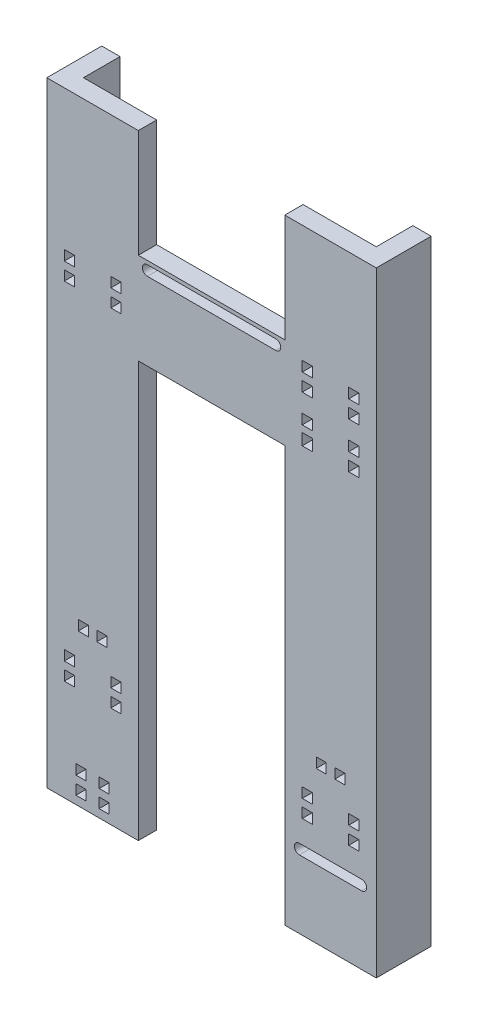
SolidWorks part; units mm, degrees
ref_plane "Front Plane" through (0, 0, 0) normal (0, 0, 1) x (1, 0, 0)
ref_plane "Top Plane" through (0, 0, 0) normal (0, 1, 0) x (1, 0, 0)
ref_plane "Right Plane" through (0, 0, 0) normal (1, 0, 0) x (0, 0, -1)
sketch "Sketch2" plane through (0, 0, 0) normal (0, 0, 1) x (1, 0, 0)
  line L1 (12.5, 84) -> (-12.5, 84)
  line L2 (12.5, 84) -> (12.5, -84)
  line L3 (12.5, -84) -> (-12.5, -84)
  line L4 (-12.5, 84) -> (-12.5, -84)
  line L5 (12.5, 84) -> (-12.5, -84) construction
  line L6 (12.5, -84) -> (-12.5, 84) construction
  point P0 (0, 0)
  dimension "D1" = 168
  dimension "D2" = 25
extrude "Boss-Extrude1" add sketch "Sketch2" along normal blind 5
sketch "Sketch3" plane through (-12.5, 0, 0) normal (-1, 0, 0) x (0, 0, 1)
  line L0 (5, -84) -> (0, -84) construction
  line L1 (0, 84) -> (-10, 84)
  line L2 (0, 84) -> (0, -84)
  line L3 (0, -84) -> (-10, -84)
  line L4 (-10, 84) -> (-10, -84)
  dimension "D1" = 10
  dimension "D2" = 0
extrude "Boss-Extrude2" add sketch "Sketch3" against normal blind 5
sketch "Sketch4" plane through (0, 0, 5) normal (0, 0, 1) x (1, 0, 0)
  line L0 (12.5, 0) -> (12.5, 84) construction
  line L1 (12.5, -84) -> (12.5, 84) construction
  line L2 (12.5, 54.5) -> (12.5, 29.5)
  line L4 (12.5, 54.5) -> (52.5, 54.5)
  line L5 (12.5, 54.5) -> (12.5, 29.5)
  line L6 (12.5, 29.5) -> (52.5, 29.5)
  line L7 (52.5, 54.5) -> (52.5, 29.5)
  point P8 (12.5, 42)
  line M5 (12.5, -84) -> (12.5, 84)
  dimension "D1" = 25
  dimension "D2" = 40
extrude "Boss-Extrude3" add sketch "Sketch4" against normal blind 5 contours L7 L4 L6 M5
sketch "Sketch5" plane through (0, 0, 5) normal (0, 0, 1) x (1, 0, 0)
  line L0 (52.5, 54.5) -> (52.5, 87.2525) construction
  line L2 (12.5, 84) -> (52.5, 84) construction
  line L3 (-12.5, -84) -> (12.5, -84) construction
  line L4 (52.5, 84) -> (77.5, 84)
  line L5 (52.5, 84) -> (52.5, -84)
  line L6 (52.5, -84) -> (77.5, -84)
  line L7 (77.5, 84) -> (77.5, -84)
  dimension "D1" = 25
  dimension "D2" = 0
extrude "Boss-Extrude4" add sketch "Sketch5" against normal blind 5
sketch "Sketch6" plane through (77.5, 0, 0) normal (1, 0, 0) x (0, 0, -1)
  line L0 (10, -84) -> (0, -84) construction
  line L1 (0, 84) -> (10, 84)
  line L2 (0, 84) -> (0, -84)
  line L3 (0, -84) -> (10, -84)
  line L4 (10, 84) -> (10, -84)
  line L5 (10, 84) -> (10, -84) construction
extrude "Boss-Extrude5" add sketch "Sketch6" against normal blind 5
sketch "Sketch7" plane through (0, 0, 5) normal (0, 0, 1) x (1, 0, 0)
  line L0 (14.9659, 52.125) -> (50.0341, 52.125) construction
  line L1 (14.9659, 53.5) -> (50.0341, 53.5)
  line L2 (14.9659, 50.75) -> (50.0341, 50.75)
  line L3 (12.5, 54.5) -> (52.5, 54.5) construction
  arc A0 (14.9659, 53.5) -> (14.9659, 50.75) centre (14.9659, 52.125) ccw
  arc A1 (50.0341, 50.75) -> (50.0341, 53.5) centre (50.0341, 52.125) ccw
  point P2 (32.5, 52.125)
  dimension "D1" = 2.75
  dimension "D2" = 1
extrude "Cut-Extrude1" cut sketch "Sketch7" against normal blind 5
sketch "Sketch8" plane through (0, 0, 5) normal (0, 0, 1) x (1, 0, 0)
  line L0 (73.5006, -64) -> (56.4994, -64) construction
  line L1 (73.5006, -65.375) -> (56.4994, -65.375)
  line L2 (73.5006, -62.625) -> (56.4994, -62.625)
  line L3 (52.5, -84) -> (77.5, -84) construction
  arc A0 (73.5006, -65.375) -> (73.5006, -62.625) centre (73.5006, -64) ccw
  arc A1 (56.4994, -62.625) -> (56.4994, -65.375) centre (56.4994, -64) ccw
  point P2 (65, -64)
  dimension "D1" = 2.75
  dimension "D2" = 20
extrude "Cut-Extrude2" cut sketch "Sketch8" against normal blind 20
sketch "Sketch9" plane through (0, 0, 5) normal (0, 0, 1) x (1, 0, 0)
  line L0 (12.5, 29.5) -> (12.5, 54.5) construction
  line L1 (12.5, 54.5) -> (12.5, 42) construction
  line L2 (12.5, 42) -> (-12.5, 42) construction
  line L3 (-12.5, 84) -> (-12.5, -84) construction
  line L4 (0, 42) -> (12.5, 42) construction
  line L5 (0, 42) -> (-12.5, 42) construction
  line L6 (12.5, 44.3813) -> (-12.5, 44.3813) construction
  line L7 (12.5, 39.6188) -> (-12.5, 39.6188) construction
  line L9 (7.725, 45.7563) -> (4.975, 45.7563)
  line L10 (7.725, 45.7563) -> (7.725, 43.0063)
  line L11 (7.725, 43.0063) -> (4.975, 43.0063)
  line L12 (4.975, 45.7563) -> (4.975, 43.0063)
  line L13 (7.725, 45.7563) -> (4.975, 43.0063) construction
  line L14 (7.725, 43.0063) -> (4.975, 45.7563) construction
  line L15 (-4.975, 45.7563) -> (-7.725, 45.7563)
  line L16 (-4.975, 45.7563) -> (-4.975, 43.0063)
  line L17 (-4.975, 43.0063) -> (-7.725, 43.0063)
  line L18 (-7.725, 45.7563) -> (-7.725, 43.0063)
  line L19 (-4.975, 45.7563) -> (-7.725, 43.0063) construction
  line L20 (-4.975, 43.0063) -> (-7.725, 45.7563) construction
  line L21 (-7.725, 40.9635) -> (-4.975, 40.9635)
  line L22 (-7.725, 40.9635) -> (-7.725, 38.274)
  line L23 (-7.725, 38.274) -> (-4.975, 38.274)
  line L24 (-4.975, 40.9635) -> (-4.975, 38.274)
  line L25 (-7.725, 40.9635) -> (-4.975, 38.274) construction
  line L26 (-7.725, 38.274) -> (-4.975, 40.9635) construction
  line L27 (4.975, 40.9635) -> (7.725, 40.9635)
  line L28 (4.975, 40.9635) -> (4.975, 38.274)
  line L29 (4.975, 38.274) -> (7.725, 38.274)
  line L30 (7.725, 40.9635) -> (7.725, 38.274)
  line L31 (4.975, 40.9635) -> (7.725, 38.274) construction
  line L32 (4.975, 38.274) -> (7.725, 40.9635) construction
  circle A0 centre (6.35, 39.6188) radius 1.375 construction
  circle A1 centre (-6.35, 39.6188) radius 1.375 construction
  circle A2 centre (6.35, 44.3813) radius 1.375 construction
  circle A3 centre (-6.35, 44.3813) radius 1.375 construction
  point P17 (0, 39.6188)
  dimension "D5" = 2.75
  dimension "D6" = 2.75
  dimension "D7" = 2.75
  dimension "D8" = 2.75
  dimension "D1" = 2.3813
  dimension "D2" = 2.3813
  dimension "D3" = 6.35
  dimension "D4" = 6.35
extrude "Cut-Extrude3" cut sketch "Sketch9" against normal blind 20
sketch "Sketch10" plane through (0, 0, 5) normal (0, 0, 1) x (1, 0, 0)
  line L0 (52.5, 54.5) -> (52.5, 29.5) construction
  line L1 (52.5, 29.5) -> (52.5, 42) construction
  line L2 (52.5, 42) -> (52.5, 35.75) construction
  line L3 (52.5, 35.75) -> (77.5, 35.75) construction
  line L4 (77.5, -84) -> (77.5, 84) construction
  line L5 (52.5, 54.5) -> (52.5, 42) construction
  line L6 (52.5, 42) -> (52.5, 48.25) construction
  line L7 (52.5, 48.25) -> (77.5, 48.25) construction
  line L8 (52.5, 50.6313) -> (77.5, 50.6313) construction
  line L9 (52.5, 45.8688) -> (77.5, 45.8688) construction
  line L10 (52.5, 38.1313) -> (77.5, 38.1313) construction
  line L11 (52.5, 33.3688) -> (77.5, 33.3688) construction
  line L14 (57.275, 52.0063) -> (60.025, 52.0063)
  line L15 (57.275, 52.0063) -> (57.275, 49.2563)
  line L16 (57.275, 49.2563) -> (60.025, 49.2563)
  line L17 (60.025, 52.0063) -> (60.025, 49.2563)
  line L18 (57.275, 52.0063) -> (60.025, 49.2563) construction
  line L19 (57.275, 49.2563) -> (60.025, 52.0063) construction
  line L20 (69.975, 52.0063) -> (72.725, 52.0063)
  line L21 (69.975, 52.0063) -> (69.975, 49.2563)
  line L22 (69.975, 49.2563) -> (72.725, 49.2563)
  line L23 (72.725, 52.0063) -> (72.725, 49.2563)
  line L24 (69.975, 52.0063) -> (72.725, 49.2563) construction
  line L25 (69.975, 49.2563) -> (72.725, 52.0063) construction
  line L26 (57.275, 47.2438) -> (60.025, 47.2438)
  line L27 (57.275, 47.2438) -> (57.275, 44.4938)
  line L28 (57.275, 44.4938) -> (60.025, 44.4938)
  line L29 (60.025, 47.2438) -> (60.025, 44.4938)
  line L30 (57.275, 47.2438) -> (60.025, 44.4938) construction
  line L31 (57.275, 44.4938) -> (60.025, 47.2438) construction
  line L32 (69.975, 47.2438) -> (72.725, 47.2438)
  line L33 (69.975, 47.2438) -> (69.975, 44.4938)
  line L34 (69.975, 44.4938) -> (72.725, 44.4938)
  line L35 (72.725, 47.2438) -> (72.725, 44.4938)
  line L36 (69.975, 47.2438) -> (72.725, 44.4938) construction
  line L37 (69.975, 44.4938) -> (72.725, 47.2438) construction
  line L38 (69.975, 39.5063) -> (72.725, 39.5063)
  line L39 (69.975, 39.5063) -> (69.975, 36.7563)
  line L40 (69.975, 36.7563) -> (72.725, 36.7563)
  line L41 (72.725, 39.5063) -> (72.725, 36.7563)
  line L42 (69.975, 39.5063) -> (72.725, 36.7563) construction
  line L43 (69.975, 36.7563) -> (72.725, 39.5063) construction
  line L44 (57.275, 39.5063) -> (60.025, 39.5063)
  line L45 (57.275, 39.5063) -> (57.275, 36.7563)
  line L46 (57.275, 36.7563) -> (60.025, 36.7563)
  line L47 (60.025, 39.5063) -> (60.025, 36.7563)
  line L48 (57.275, 39.5063) -> (60.025, 36.7563) construction
  line L49 (57.275, 36.7563) -> (60.025, 39.5063) construction
  line L50 (57.275, 34.9438) -> (60.025, 34.9438)
  line L51 (57.275, 34.9438) -> (57.275, 31.7938)
  line L52 (57.275, 31.7938) -> (60.025, 31.7938)
  line L53 (60.025, 34.9438) -> (60.025, 31.7938)
  line L54 (57.275, 34.9438) -> (60.025, 31.7938) construction
  line L55 (57.275, 31.7938) -> (60.025, 34.9438) construction
  line L56 (69.975, 34.7438) -> (72.725, 34.7438)
  line L57 (69.975, 34.7438) -> (69.975, 31.9938)
  line L58 (69.975, 31.9938) -> (72.725, 31.9938)
  line L59 (72.725, 34.7438) -> (72.725, 31.9938)
  line L60 (69.975, 34.7438) -> (72.725, 31.9938) construction
  line L61 (69.975, 31.9938) -> (72.725, 34.7438) construction
  circle A0 centre (71.35, 33.3688) radius 1.375 construction
  circle A1 centre (58.65, 33.3688) radius 1.375 construction
  circle A2 centre (58.65, 38.1313) radius 1.375 construction
  circle A3 centre (71.35, 38.1313) radius 1.375 construction
  circle A4 centre (71.35, 45.8688) radius 1.375 construction
  circle A5 centre (58.65, 45.8688) radius 1.375 construction
  circle A6 centre (58.65, 50.6313) radius 1.375 construction
  circle A7 centre (71.35, 50.6313) radius 1.375 construction
  point P23 (65, 33.3688)
  dimension "D7" = 2.75
  dimension "D8" = 2.75
  dimension "D9" = 2.75
  dimension "D10" = 2.75
  dimension "D11" = 2.75
  dimension "D12" = 2.75
  dimension "D13" = 2.75
  dimension "D14" = 2.75
  dimension "D1" = 2.3813
  dimension "D2" = 2.3813
  dimension "D3" = 2.3813
  dimension "D4" = 2.3813
  dimension "D5" = 6.35
  dimension "D6" = 6.35
extrude "Cut-Extrude4" cut sketch "Sketch10" against normal blind 20
sketch "Sketch11" plane through (0, 0, 5) normal (0, 0, 1) x (1, 0, 0)
  line L0 (-12.5, -52.625) -> (12.5, -52.625) construction
  line L1 (-12.5, 84) -> (-12.5, -84) construction
  line L2 (12.5, -84) -> (12.5, 29.5) construction
  line L3 (52.5, -52.625) -> (77.5, -52.625) construction
  line L4 (52.5, 29.5) -> (52.5, -84) construction
  line L5 (77.5, -84) -> (77.5, 84) construction
  line L6 (12.5, -50.2437) -> (-12.5, -50.2437) construction
  line L7 (-12.5, -55.0062) -> (12.5, -55.0062) construction
  line L8 (52.5, -55.0062) -> (77.5, -55.0062) construction
  line L9 (52.5, -50.2437) -> (77.5, -50.2437) construction
  line L10 (73.5006, -62.625) -> (56.4994, -62.625) construction
  line L12 (60.025, -48.8687) -> (57.275, -48.8687)
  line L13 (60.025, -48.8687) -> (60.025, -51.6187)
  line L14 (60.025, -51.6187) -> (57.275, -51.6187)
  line L15 (57.275, -48.8687) -> (57.275, -51.6187)
  line L16 (60.025, -48.8687) -> (57.275, -51.6187) construction
  line L17 (60.025, -51.6187) -> (57.275, -48.8687) construction
  line L18 (72.741, -48.8687) -> (69.959, -48.8687)
  line L19 (72.741, -48.8687) -> (72.741, -51.6187)
  line L20 (72.741, -51.6187) -> (69.959, -51.6187)
  line L21 (69.959, -48.8687) -> (69.959, -51.6187)
  line L22 (72.741, -48.8687) -> (69.959, -51.6187) construction
  line L23 (72.741, -51.6187) -> (69.959, -48.8687) construction
  line L24 (69.98, -53.6362) -> (72.72, -53.6362)
  line L25 (69.98, -53.6362) -> (69.98, -56.3762)
  line L26 (69.98, -56.3762) -> (72.72, -56.3762)
  line L27 (72.72, -53.6362) -> (72.72, -56.3762)
  line L28 (69.98, -53.6362) -> (72.72, -56.3762) construction
  line L29 (69.98, -56.3762) -> (72.72, -53.6362) construction
  line L30 (57.275, -53.6362) -> (60.025, -53.6362)
  line L31 (57.275, -53.6362) -> (57.275, -56.3762)
  line L32 (57.275, -56.3762) -> (60.025, -56.3762)
  line L33 (60.025, -53.6362) -> (60.025, -56.3762)
  line L34 (57.275, -53.6362) -> (60.025, -56.3762) construction
  line L35 (57.275, -56.3762) -> (60.025, -53.6362) construction
  line L36 (-7.725, -48.8687) -> (-4.975, -48.8687)
  line L37 (-7.725, -48.8687) -> (-7.725, -51.6187)
  line L38 (-7.725, -51.6187) -> (-4.975, -51.6187)
  line L39 (-4.975, -48.8687) -> (-4.975, -51.6187)
  line L40 (-7.725, -48.8687) -> (-4.975, -51.6187) construction
  line L41 (-7.725, -51.6187) -> (-4.975, -48.8687) construction
  line L42 (4.975, -48.8687) -> (7.725, -48.8687)
  line L43 (4.975, -48.8687) -> (4.975, -51.6187)
  line L44 (4.975, -51.6187) -> (7.725, -51.6187)
  line L45 (7.725, -48.8687) -> (7.725, -51.6187)
  line L46 (4.975, -48.8687) -> (7.725, -51.6187) construction
  line L47 (4.975, -51.6187) -> (7.725, -48.8687) construction
  line L48 (4.975, -53.6362) -> (7.725, -53.6362)
  line L49 (4.975, -53.6362) -> (4.975, -56.3762)
  line L50 (4.975, -56.3762) -> (7.725, -56.3762)
  line L51 (7.725, -53.6362) -> (7.725, -56.3762)
  line L52 (4.975, -53.6362) -> (7.725, -56.3762) construction
  line L53 (4.975, -56.3762) -> (7.725, -53.6362) construction
  line L54 (-7.725, -53.6362) -> (-4.975, -53.6362)
  line L55 (-7.725, -53.6362) -> (-7.725, -56.3762)
  line L56 (-7.725, -56.3762) -> (-4.975, -56.3762)
  line L57 (-4.975, -53.6362) -> (-4.975, -56.3762)
  line L58 (-7.725, -53.6362) -> (-4.975, -56.3762) construction
  line L59 (-7.725, -56.3762) -> (-4.975, -53.6362) construction
  circle A0 centre (-6.35, -50.2437) radius 1.375 construction
  circle A1 centre (6.35, -50.2437) radius 1.375 construction
  circle A2 centre (-6.35, -55.0062) radius 1.375 construction
  circle A3 centre (6.35, -55.0062) radius 1.375 construction
  circle A4 centre (58.65, -50.2437) radius 1.375 construction
  circle A5 centre (71.35, -50.2437) radius 1.375 construction
  circle A6 centre (58.65, -55.0062) radius 1.375 construction
  circle A7 centre (71.35, -55.0062) radius 1.37 construction
  point P26 (0, -50.2437)
  point P35 (65, -50.2437)
  dimension "D6" = 2.75
  dimension "D7" = 2.75
  dimension "D8" = 2.75
  dimension "D9" = 2.75
  dimension "D12" = 2.75
  dimension "D13" = 2.75
  dimension "D14" = 2.75
  dimension "D15" = 2.74
  dimension "D1" = 2.3813
  dimension "D2" = 2.3813
  dimension "D3" = 10
  dimension "D4" = 6.35
  dimension "D5" = 6.35
  dimension "D10" = 6.35
  dimension "D11" = 6.35
extrude "Cut-Extrude5" cut sketch "Sketch11" against normal blind 20
sketch "Sketch12" plane through (0, 0, 5) normal (0, 0, 1) x (1, 0, 0)
  line L0 (-12.5, -78.0251) -> (12.5, -78.0251) construction
  line L1 (-12.5, 84) -> (-12.5, -84) construction
  line L2 (12.5, -84) -> (12.5, 29.5) construction
  line L3 (12.5, -75.6438) -> (-12.5, -75.6438) construction
  line L4 (12.5, -80.4063) -> (-12.5, -80.4063) construction
  line L6 (-1.8, -74.2688) -> (-4.55, -74.2688)
  line L7 (-1.8, -74.2688) -> (-1.8, -77.0188)
  line L8 (-1.8, -77.0188) -> (-4.55, -77.0188)
  line L9 (-4.55, -74.2688) -> (-4.55, -77.0188)
  line L10 (-1.8, -74.2688) -> (-4.55, -77.0188) construction
  line L11 (-1.8, -77.0188) -> (-4.55, -74.2688) construction
  line L12 (4.55, -74.2688) -> (1.8, -74.2688)
  line L13 (4.55, -74.2688) -> (4.55, -77.0188)
  line L14 (4.55, -77.0188) -> (1.8, -77.0188)
  line L15 (1.8, -74.2688) -> (1.8, -77.0188)
  line L16 (4.55, -74.2688) -> (1.8, -77.0188) construction
  line L17 (4.55, -77.0188) -> (1.8, -74.2688) construction
  line L18 (1.8, -79.0313) -> (4.55, -79.0313)
  line L19 (1.8, -79.0313) -> (1.8, -81.7813)
  line L20 (1.8, -81.7813) -> (4.55, -81.7813)
  line L21 (4.55, -79.0313) -> (4.55, -81.7813)
  line L22 (1.8, -79.0313) -> (4.55, -81.7813) construction
  line L23 (1.8, -81.7813) -> (4.55, -79.0313) construction
  line L24 (-4.55, -79.0313) -> (-1.8, -79.0313)
  line L25 (-4.55, -79.0313) -> (-4.55, -81.7813)
  line L26 (-4.55, -81.7813) -> (-1.8, -81.7813)
  line L27 (-1.8, -79.0313) -> (-1.8, -81.7813)
  line L28 (-4.55, -79.0313) -> (-1.8, -81.7813) construction
  line L29 (-4.55, -81.7813) -> (-1.8, -79.0313) construction
  circle A0 centre (-3.175, -75.6438) radius 1.375 construction
  circle A1 centre (3.175, -75.6438) radius 1.375 construction
  circle A2 centre (-3.175, -80.4063) radius 1.375 construction
  circle A3 centre (3.175, -80.4063) radius 1.375 construction
  point P14 (0, -75.6438)
  dimension "D5" = 2.75
  dimension "D6" = 2.75
  dimension "D7" = 2.75
  dimension "D8" = 2.75
  dimension "D1" = 2.3813
  dimension "D2" = 2.3813
  dimension "D3" = 3.175
  dimension "D4" = 3.175
extrude "Cut-Extrude6" cut sketch "Sketch12" against normal blind 20
sketch "Sketch13" plane through (0, 0, 5) normal (0, 0, 1) x (1, 0, 0)
  line L0 (-12.5, -41.2371) -> (12.5, -41.2371) construction
  line L1 (-12.5, 84) -> (-12.5, -84) construction
  line L2 (12.5, -84) -> (12.5, 29.5) construction
  line L3 (52.5, -41.2371) -> (77.5, -41.2371) construction
  line L4 (52.5, 29.5) -> (52.5, -84) construction
  line L5 (77.5, -84) -> (77.5, 84) construction
  line L7 (-1.165, -39.8621) -> (-3.915, -39.8621)
  line L8 (-1.165, -39.8621) -> (-1.165, -42.6121)
  line L9 (-1.165, -42.6121) -> (-3.915, -42.6121)
  line L10 (-3.915, -39.8621) -> (-3.915, -42.6121)
  line L11 (-1.165, -39.8621) -> (-3.915, -42.6121) construction
  line L12 (-1.165, -42.6121) -> (-3.915, -39.8621) construction
  line L13 (1.165, -39.8621) -> (3.915, -39.8621)
  line L14 (1.165, -39.8621) -> (1.165, -42.6121)
  line L15 (1.165, -42.6121) -> (3.915, -42.6121)
  line L16 (3.915, -39.8621) -> (3.915, -42.6121)
  line L17 (1.165, -39.8621) -> (3.915, -42.6121) construction
  line L18 (1.165, -42.6121) -> (3.915, -39.8621) construction
  line L19 (63.8098, -39.8621) -> (61.1102, -39.8621)
  line L20 (63.8098, -39.8621) -> (63.8098, -42.6121)
  line L21 (63.8098, -42.6121) -> (61.1102, -42.6121)
  line L22 (61.1102, -39.8621) -> (61.1102, -42.6121)
  line L23 (63.8098, -39.8621) -> (61.1102, -42.6121) construction
  line L24 (63.8098, -42.6121) -> (61.1102, -39.8621) construction
  line L25 (66.165, -39.8621) -> (68.915, -39.8621)
  line L26 (66.165, -39.8621) -> (66.165, -42.6121)
  line L27 (66.165, -42.6121) -> (68.915, -42.6121)
  line L28 (68.915, -39.8621) -> (68.915, -42.6121)
  line L29 (66.165, -39.8621) -> (68.915, -42.6121) construction
  line L30 (66.165, -42.6121) -> (68.915, -39.8621) construction
  circle A0 centre (-2.54, -41.2371) radius 1.375 construction
  circle A1 centre (2.54, -41.2371) radius 1.375 construction
  circle A2 centre (62.46, -41.2371) radius 1.375 construction
  circle A3 centre (67.54, -41.2371) radius 1.375 construction
  point P20 (0, -41.2371)
  point P21 (65, -41.2371)
  dimension "D2" = 2.75
  dimension "D4" = 2.75
  dimension "D6" = 2.75
  dimension "D7" = 2.75
  dimension "D1" = 2.54
  dimension "D3" = 2.54
  dimension "D5" = 2.54
  dimension "D8" = 2.54
extrude "Cut-Extrude7" cut sketch "Sketch13" against normal blind 20
